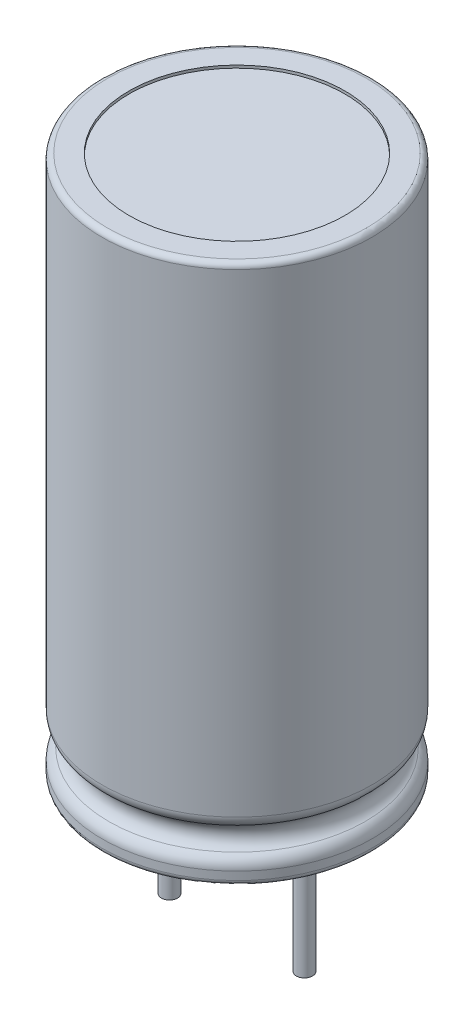
SolidWorks part; units mm, degrees
ref_plane "Front Plane" through (0, 0, 0) normal (0, 0, 1) x (1, 0, 0)
ref_plane "Top Plane" through (0, 0, 0) normal (0, 1, 0) x (1, 0, 0)
ref_plane "Right Plane" through (0, 0, 0) normal (1, 0, 0) x (0, 0, -1)
sketch "Sketch1" plane through (0, 0, 0) normal (0, 0, 1) x (1, 0, 0)
  line L0 (0, 0) -> (0, 20)
  line L1 (0, 20) -> (-5, 20)
  line L2 (-5, 20) -> (-5, 2.2321)
  line L7 (-5, 0) -> (0, 0)
  line L8 (-5, 0.5) -> (-5, 0)
  arc A0 (-5, 2.2321) -> (-4.75, 1.799) centre (-4.5, 2.2321) ccw
  arc A1 (-4.75, 1.799) -> (-4.75, 0.933) centre (-5, 1.366) cw
  arc A2 (-4.75, 0.933) -> (-5, 0.5) centre (-4.5, 0.5) ccw
  point P12 (-4.9013, 1.9492)
  point P13 (0, 0)
  point P14 (-4.4929, 1.3257)
  point P15 (-5, 1.3787)
  point P16 (-4.8001, 1.4056)
  point P17 (-5, 1.3684)
  dimension "D3" = 0.5
  dimension "D4" = 0.5
  dimension "D1" = 5
  dimension "D2" = 20
  dimension "D5" = 0.5
revolve "Revolve1" add sketch "Sketch1" angle 360 about L0
fillet "Fillet2" radius 0.2 2 edges at (0, 0, -5) (0, 20, -5)
sketch "Sketch3" plane through (0, 20, 0) normal (0, 1, 0) x (1, 0, 0)
  line L0 (-4, 0) -> (-5, 0) construction
  circle A2 centre (0, 0) radius 4
  point P3 (-5, 0)
  dimension "D1" = 1
extrude "Cut-Extrude1" cut sketch "Sketch3" against normal blind 0.1
sketch "Sketch4" plane through (0, 0, 0) normal (0, -1, 0) x (1, 0, 0)
  circle A0 centre (0, 0) radius 4
extrude "Cut-Extrude2" cut sketch "Sketch4" against normal blind 0.1
sketch "Sketch2" plane through (0, 0, 0) normal (0, -1, 0) x (1, 0, 0)
  line L0 (2.5, 0) -> (-2.5, 0) construction
  circle A0 centre (-2.5, 0) radius 0.3
  circle A1 centre (2.5, 0) radius 0.3
  point P4 (0, 0)
  dimension "D2" = 0.6
  dimension "D1" = 5
extrude "Boss-Extrude1" add sketch "Sketch2" along normal mid plane 10 separate body
